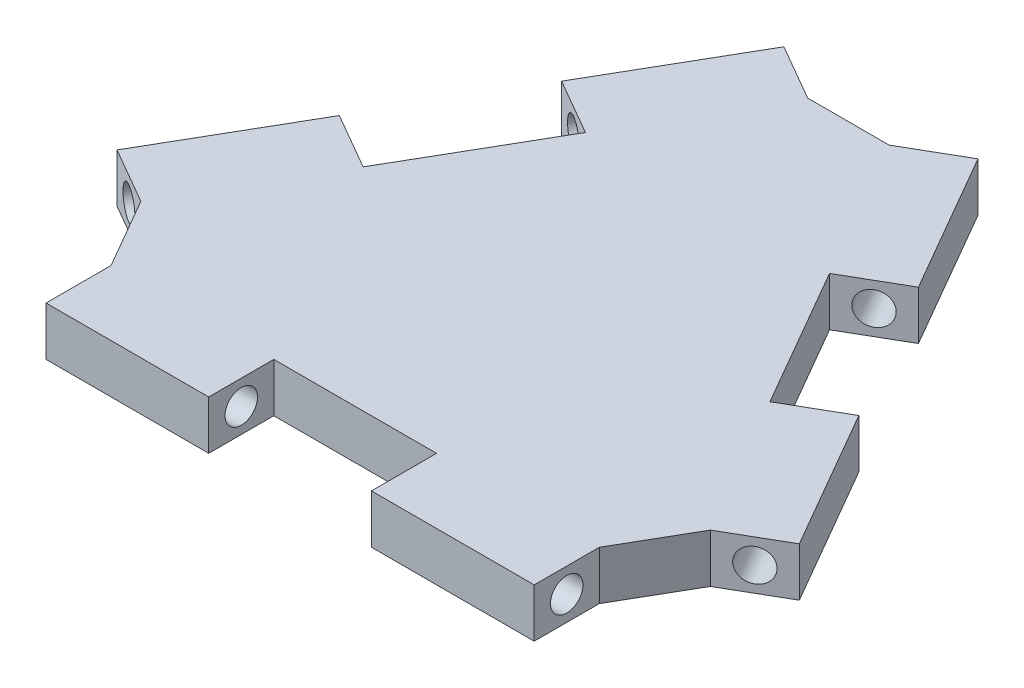
SolidWorks part; units mm, degrees
ref_plane "Front Plane" through (0, 0, 0) normal (0, 0, 1) x (1, 0, 0)
ref_plane "Top Plane" through (0, 0, 0) normal (0, 1, 0) x (1, 0, 0)
ref_plane "Right Plane" through (0, 0, 0) normal (1, 0, 0) x (0, 0, -1)
sketch "Sketch1" plane through (0, 0, 0) normal (0, 1, 0) x (1, 0, 0)
  line L0 (0, 34.641) -> (-2.5, 30.3109)
  line L1 (-20, 0) -> (-15, 0)
  line L2 (20, 0) -> (17.5, 4.3301)
  line L3 (2.5, 30.3109) -> (5.9641, 32.3109)
  line L4 (5.9641, 32.3109) -> (10.9641, 23.6506)
  line L5 (10.9641, 23.6506) -> (7.5, 21.6506)
  line L6 (10, 17.3205) -> (27.0259, 27.1504) construction
  line L7 (15.9641, 14.9904) -> (12.5, 12.9904)
  line L8 (20.9641, 6.3301) -> (15.9641, 14.9904)
  line L9 (17.5, 4.3301) -> (20.9641, 6.3301)
  line L10 (0, 34.641) -> (0, 0) construction
  line L11 (-20, 0) -> (10, 17.3205) construction
  line L12 (-17.5, 4.3301) -> (-20.9641, 6.3301)
  line L13 (-20.9641, 6.3301) -> (-15.9641, 14.9904)
  line L14 (-15.9641, 14.9904) -> (-12.5, 12.9904)
  line L15 (-10.9641, 23.6506) -> (-7.5, 21.6506)
  line L16 (-5.9641, 32.3109) -> (-10.9641, 23.6506)
  line L17 (-2.5, 30.3109) -> (-5.9641, 32.3109)
  line L18 (-15, 0) -> (-15, -4)
  line L19 (-15, -4) -> (-5, -4)
  line L20 (-5, -4) -> (-5, 0)
  line L21 (5, -4) -> (5, 0)
  line L22 (15, -4) -> (5, -4)
  line L23 (15, 0) -> (15, -4)
  line L24 (-7.5, 21.6506) -> (-12.5, 12.9904)
  line L25 (2.5, 30.3109) -> (0, 34.641)
  line L26 (12.5, 12.9904) -> (7.5, 21.6506)
  line L27 (15, 0) -> (20, 0)
  line L28 (-5, 0) -> (5, 0)
  line L29 (-17.5, 4.3301) -> (-20, 0)
  dimension "D1" = 40
  dimension "D2" = 5
  dimension "D3" = 10
  dimension "D4" = 4
  dimension "D5" = 10
  dimension "D6" = 34.641
extrude "Boss-Extrude1" add sketch "Sketch1" along normal blind 3 contours L0 L17 L16 L15 | L14 L13 L12 L0 | L1 L2 L0 | L5 L4 L3 L2 | L2 L9 L8 L7 | L23 L1 L21 L22 | L19 L20 L1 L18
pattern_linear "LPattern1" [suppressed] count 7 spacing 50
sketch "Sketch3" plane through (0, 3, 0) normal (0, 1, 0) x (1, 0, 0)
  line L0 (-20, 0) -> (-15, 0) construction
  line L1 (-17.5, 4.3301) -> (-20, 0) construction
  line L2 (0, 34.641) -> (-2.5, 30.3109) construction
  line L3 (2.5, 30.3109) -> (0, 34.641) construction
  line L4 (20, 0) -> (17.5, 4.3301) construction
  line L5 (15, 0) -> (20, 0) construction
  line L6 (-20, 0) -> (-15, 0)
  line L7 (-17.5, 4.3301) -> (-20, 0)
  line L8 (0, 34.641) -> (-2.5, 30.3109)
  line L9 (2.5, 30.3109) -> (0, 34.641)
  line L10 (20, 0) -> (17.5, 4.3301)
  line L11 (15, 0) -> (20, 0)
  line L12 (-17.5, 4.3301) -> (-15, 0)
  line L13 (15, 0) -> (17.5, 4.3301)
  line L14 (2.5, 30.3109) -> (-2.5, 30.3109)
extrude "Cut-Extrude1" cut sketch "Sketch3" against normal blind 20
sketch "Sketch4" plane through (15, 0, 0) normal (1, 0, 0) x (0, 0, -1)
  line L0 (-2, 3) -> (-2, 0) construction
  line L1 (0, 3) -> (-4, 3) construction
  line L2 (0, 0) -> (-4, 0) construction
  line L3 (-2, 0) -> (-4, 1.5) construction
  line L4 (-4, 3) -> (-4, 0) construction
  line L5 (-4, 1.5) -> (0, 1.5) construction
  line L6 (0, 3) -> (0, 0) construction
  circle A0 centre (-2, 1.5) radius 1
  dimension "D1" = 2
extrude "Cut-Extrude2" cut sketch "Sketch4" against normal blind 63
sketch "Sketch5" plane through (2.5, 0, 4.3301) normal (0.5, 0, 0.866) x (0.866, 0, -0.5)
  line L0 (19.3205, 3) -> (19.3205, 0) construction
  line L1 (17.3205, 3) -> (21.3205, 3) construction
  line L2 (17.3205, 0) -> (21.3205, 0) construction
  line L4 (21.3205, 3) -> (21.3205, 0) construction
  line L5 (21.3205, 1.5) -> (17.3205, 1.5) construction
  line L6 (17.3205, 3) -> (17.3205, 0) construction
  circle A0 centre (19.3205, 1.5) radius 1
  dimension "D1" = 2
extrude "Cut-Extrude3" cut sketch "Sketch5" against normal blind 36
mirror "Mirror1" about plane through (0, 0, 0) normal (1, 0, 0) of "Cut-Extrude3"
